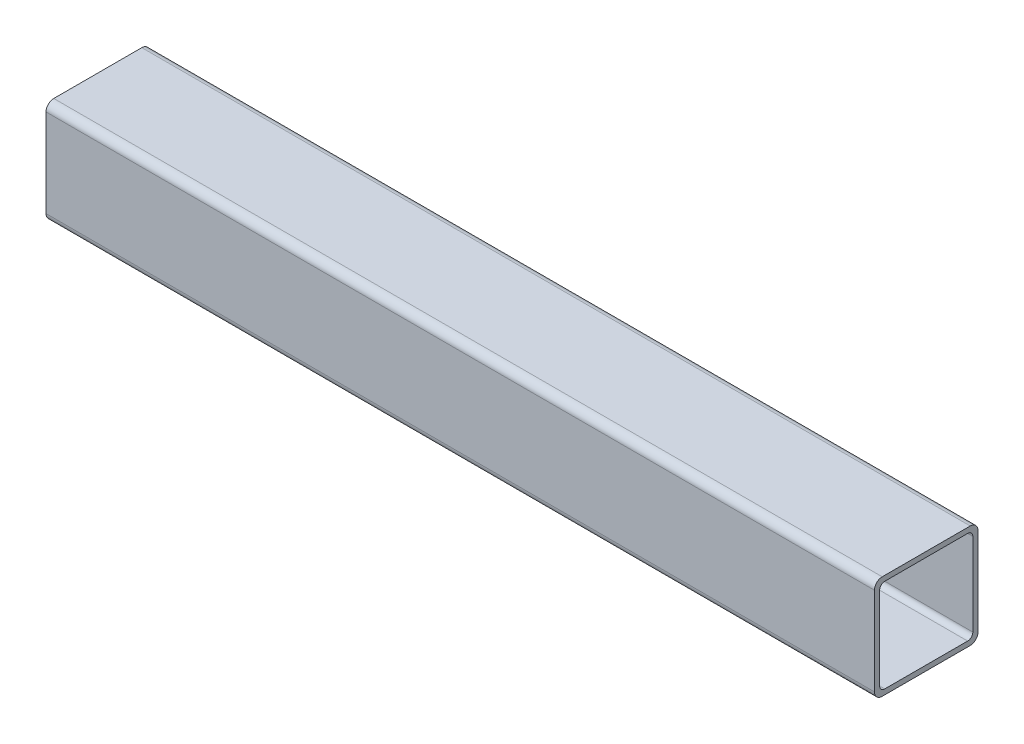
SolidWorks part; units mm, degrees
material "AISI 1020"
ref_plane "Спереди" through (0, 0, 0) normal (0, 0, 1) x (1, 0, 0)
ref_plane "Сверху" through (0, 0, 0) normal (0, 1, 0) x (1, 0, 0)
ref_plane "Справа" through (0, 0, 0) normal (1, 0, 0) x (0, 0, -1)
sketch "Эскиз1" plane through (0, 0, 0) normal (1, 0, 0) x (0, 0, -1)
  line B0 (-17, 20) -> (17, 20)
  line B1 (-20, 17) -> (-20, -17)
  line B2 (-17, -20) -> (17, -20)
  line B3 (20, 17) -> (20, -17)
  line B4 (-20, 20) -> (20, -20) construction
  line B5 (-16, 18) -> (16, 18)
  line B6 (-18, 16) -> (-18, -16)
  line B7 (-16, -18) -> (16, -18)
  line B8 (18, 16) -> (18, -16)
  line B9 (-18, 18) -> (18, -18) construction
  arc B10 (-20, -17) -> (-17, -20) centre (-17, -17) ccw
  arc B11 (17, -20) -> (20, -17) centre (17, -17) ccw
  arc B12 (17, 20) -> (20, 17) centre (17, 17) cw
  arc B13 (-17, 20) -> (-20, 17) centre (-17, 17) ccw
  arc B14 (-18, -16) -> (-16, -18) centre (-16, -16) ccw
  arc B15 (16, -18) -> (18, -16) centre (16, -16) ccw
  arc B16 (16, 18) -> (18, 16) centre (16, 16) cw
  arc B17 (-16, 18) -> (-18, 16) centre (-16, 16) ccw
sketch_block_instance "Блок-30х30х2-1"
sketch_block "Блок-30х30х2" parameters "D3"=3, "D4"=2, "D1"=40, "D2"=2
extrude "Бобышка-Вытянуть1" add sketch "Эскиз1" against normal blind 320
